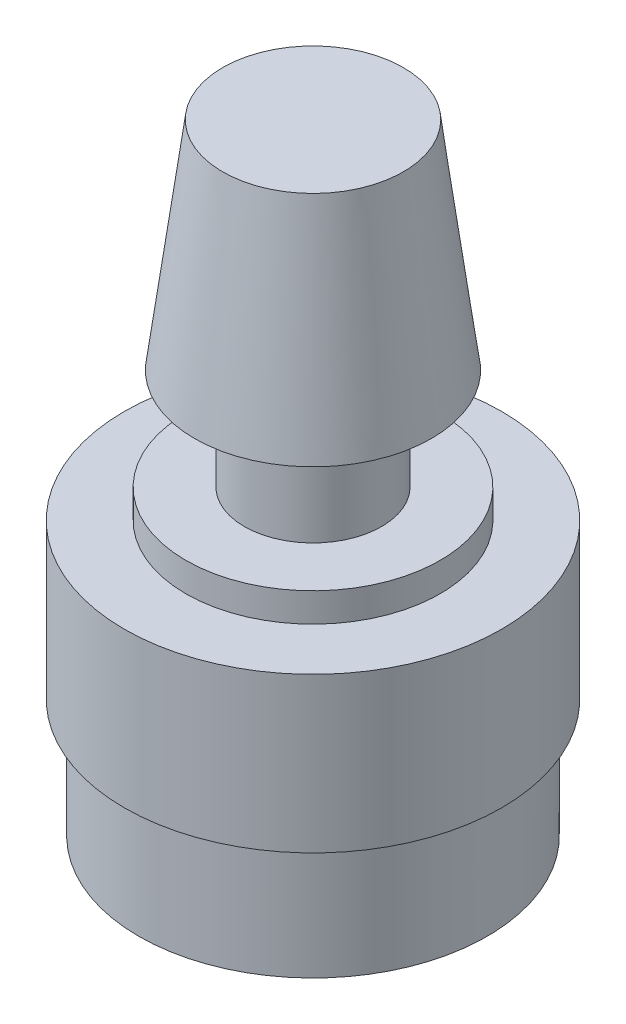
SolidWorks part; units mm, degrees
ref_plane "Plan de face" through (0, 0, 0) normal (0, 0, 1) x (1, 0, 0)
ref_plane "Plan de dessus" through (0, 0, 0) normal (0, 1, 0) x (1, 0, 0)
ref_plane "Plan de droite" through (0, 0, 0) normal (1, 0, 0) x (0, 0, -1)
sketch "Esquisse1" plane through (0, 0, 0) normal (0, 1, 0) x (1, 0, 0)
  circle A0 centre (0, 0) radius 13.05
  dimension "D1" = 26.1
extrude "Boss.-Extru.1" add sketch "Esquisse1" along normal blind 10.7
sketch "Esquisse2" plane through (0, 10.7, 0) normal (0, 1, 0) x (1, 0, 0)
  circle A0 centre (0, 0) radius 8.8
  dimension "D1" = 17.6
extrude "Boss.-Extru.2" add sketch "Esquisse2" along normal blind 2
sketch "Esquisse3" plane through (0, 12.7, 0) normal (0, 1, 0) x (1, 0, 0)
  circle A0 centre (0, 0) radius 4.75
  dimension "D1" = 9.5
extrude "Boss.-Extru.3" add sketch "Esquisse3" along normal blind 7
sketch "Esquisse5" plane through (0, 0, 0) normal (0, -1, 0) x (1, 0, 0)
  circle A0 centre (0, 0) radius 11.05
  circle A1 centre (0, 0) radius 12.05
  circle A2 centre (0, 0) radius 13.05 construction
  dimension "D1" = 1
  dimension "D2" = 1
extrude "Boss.-Extru.5" add sketch "Esquisse5" along normal blind 8.2
sketch "Esquisse6" plane through (0, 0, 0) normal (0, 0, 1) x (1, 0, 0)
  line L0 (0, 19.7) -> (8.2, 19.7)
  line L1 (4.75, 19.7) -> (-4.75, 19.7) construction
  line L2 (8.2, 19.7) -> (6.25, 34.7)
  line L3 (6.25, 34.7) -> (0, 34.7)
  line L4 (0, 34.7) -> (0, 19.7)
  dimension "D1" = 8.2
  dimension "D2" = 6.25
  dimension "D3" = 90
  dimension "D4" = 15
revolve "Révolution1" add sketch "Esquisse6" angle 360 about L4
